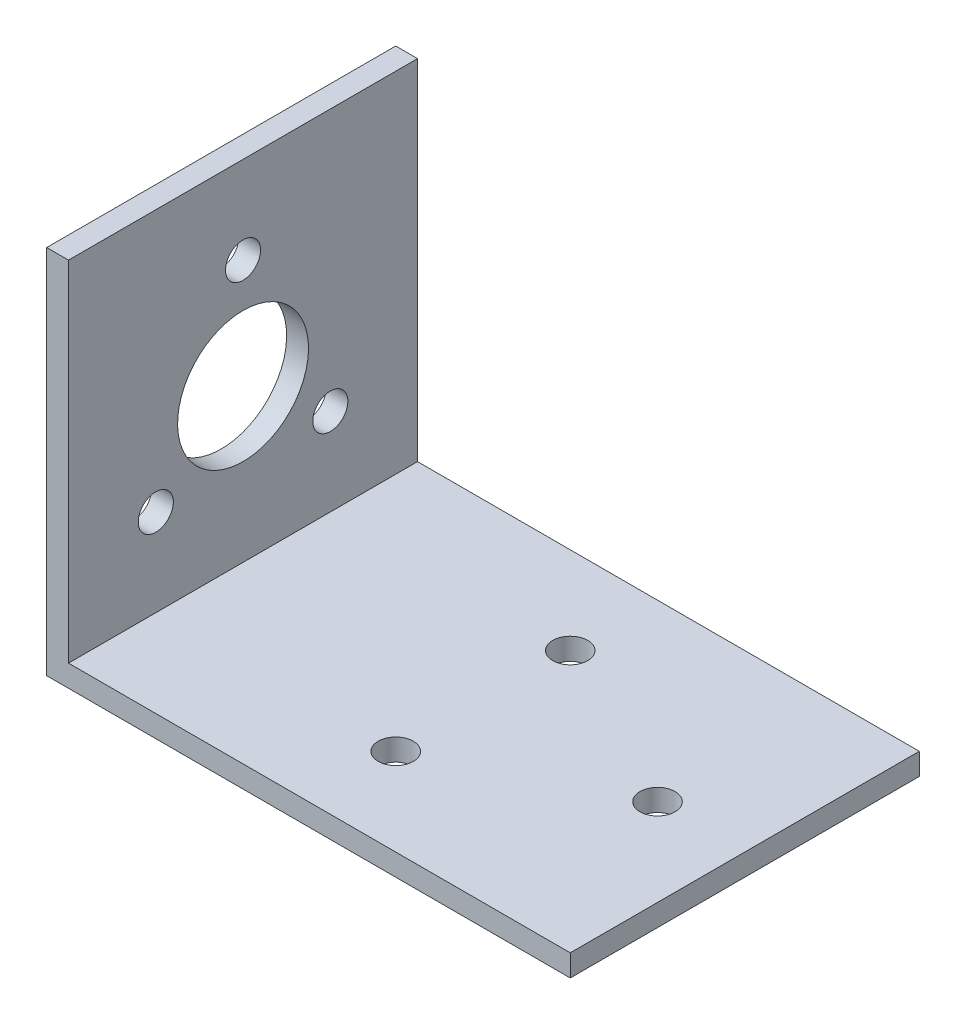
SolidWorks part; units mm, degrees
ref_plane "Front Plane" through (0, 0, 0) normal (0, 0, 1) x (1, 0, 0)
ref_plane "Top Plane" through (0, 0, 0) normal (0, 1, 0) x (1, 0, 0)
ref_plane "Right Plane" through (0, 0, 0) normal (1, 0, 0) x (0, 0, -1)
sketch "Sketch1" plane through (0, 0, 0) normal (0, 0, 1) x (1, 0, 0)
  line L1 (0, 0) -> (-3.175, 0)
  line L2 (0, 3.175) -> (0, 53.975)
  line L3 (0, 53.975) -> (-3.175, 53.975)
  line L4 (-3.175, 0) -> (-3.175, 53.975)
  line L5 (0, 0) -> (73.025, 0)
  line L7 (0, 3.175) -> (73.025, 3.175)
  line L8 (73.025, 0) -> (73.025, 3.175)
  dimension "D1" = 3.175
  dimension "D2" = 53.975
  dimension "D3" = 73.025
extrude "Boss-Extrude1" add sketch "Sketch1" along normal blind 50.8
sketch "Sketch2" plane through (0, 0, 0) normal (1, 0, 0) x (0, 0, -1)
  line L0 (-50.8, 53.975) -> (0, 53.975) construction
  line L1 (-25.4, 53.975) -> (-25.4, 3.175) construction
  line L2 (-50.8, 3.175) -> (0, 3.175) construction
  line L3 (-38.1, 15.875) -> (-12.7, 15.875) construction
  circle A0 centre (-25.4, 41.275) radius 2.5527
  circle A1 centre (-38.1, 15.875) radius 2.5527
  circle A2 centre (-12.7, 15.875) radius 2.5527
  point P8 (-25.4, 53.975)
  point P13 (-25.4, 15.875)
  dimension "D3" = 5.1054
  dimension "D1" = 12.7
  dimension "D2" = 38.1
  dimension "D4" = 25.4
extrude "Cut-Extrude1" cut sketch "Sketch2" against normal blind 50.8
sketch "Sketch3" plane through (0, 3.175, 0) normal (0, 1, 0) x (1, 0, 0)
  line L0 (73.025, -50.8) -> (73.025, 0) construction
  line L1 (73.025, -25.4) -> (0, -25.4) construction
  line L2 (0, -50.8) -> (0, 0) construction
  line L3 (34.925, -12.7) -> (34.925, -38.1) construction
  circle A0 centre (60.325, -25.4) radius 2.5527
  circle A1 centre (34.925, -12.7) radius 2.5527
  circle A2 centre (34.925, -38.1) radius 2.5527
  point P12 (34.925, -25.4)
  dimension "D3" = 5.1054
  dimension "D1" = 38.1
  dimension "D2" = 12.7
  dimension "D4" = 25.4
extrude "Cut-Extrude2" cut sketch "Sketch3" against normal blind 50.8
sketch "Sketch4" plane through (0, 0, 0) normal (1, 0, 0) x (0, 0, -1)
  line L1 (-50.8, 53.975) -> (0, 53.975) construction
  circle A0 centre (-25.4, 25.4) radius 9.525
  point P7 (-25.4, 53.975)
  dimension "D1" = 19.05
  dimension "D2" = 28.575
extrude "Cut-Extrude3" cut sketch "Sketch4" against normal blind 3.175
